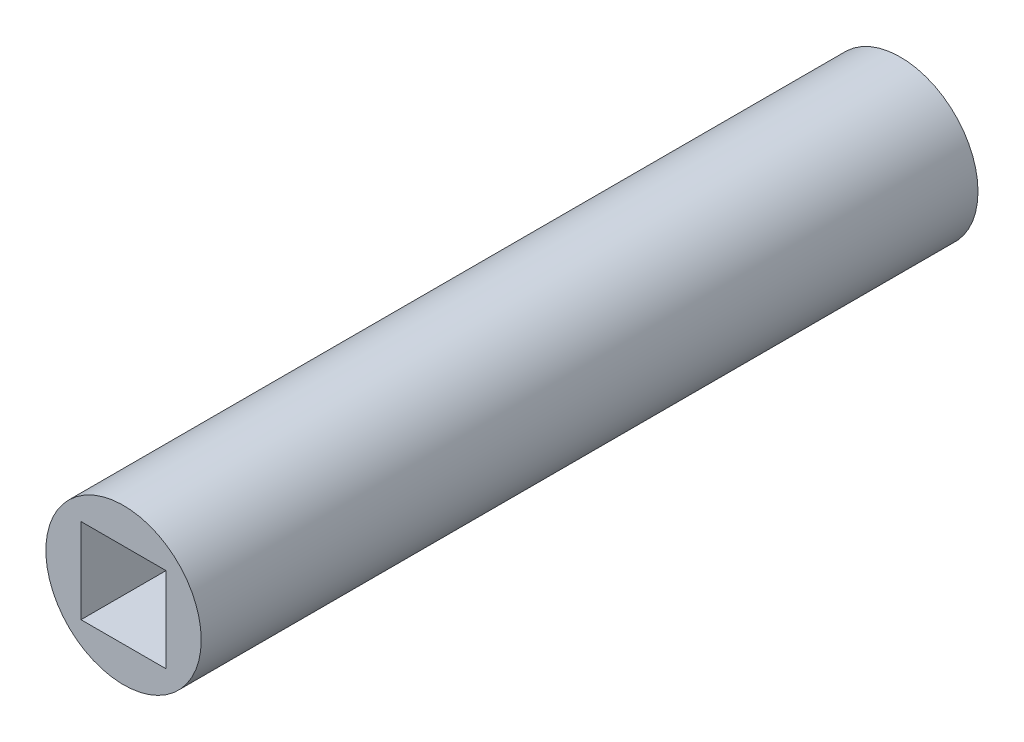
SolidWorks part; units mm, degrees
ref_plane "Front Plane" through (0, 0, 0) normal (0, 0, 1) x (1, 0, 0)
ref_plane "Top Plane" through (0, 0, 0) normal (0, 1, 0) x (1, 0, 0)
ref_plane "Right Plane" through (0, 0, 0) normal (1, 0, 0) x (0, 0, -1)
sketch "Sketch1" plane through (0, 0, 0) normal (0, 0, 1) x (1, 0, 0)
  line L1 (-1.7375, -1.7375) -> (1.7375, -1.7375)
  line L2 (-1.7375, -1.7375) -> (-1.7375, 1.7375)
  line L3 (-1.7375, 1.7375) -> (1.7375, 1.7375)
  line L4 (1.7375, -1.7375) -> (1.7375, 1.7375)
  line L5 (-1.7375, -1.7375) -> (1.7375, 1.7375) construction
  line L6 (-1.7375, 1.7375) -> (1.7375, -1.7375) construction
  circle A0 centre (0, 0) radius 3.175
  dimension "D1" = 6.35
  dimension "D2" = 3.475
  dimension "D3" = 3.475
extrude "Boss-Extrude1" add sketch "Sketch1" along normal blind 31.75
